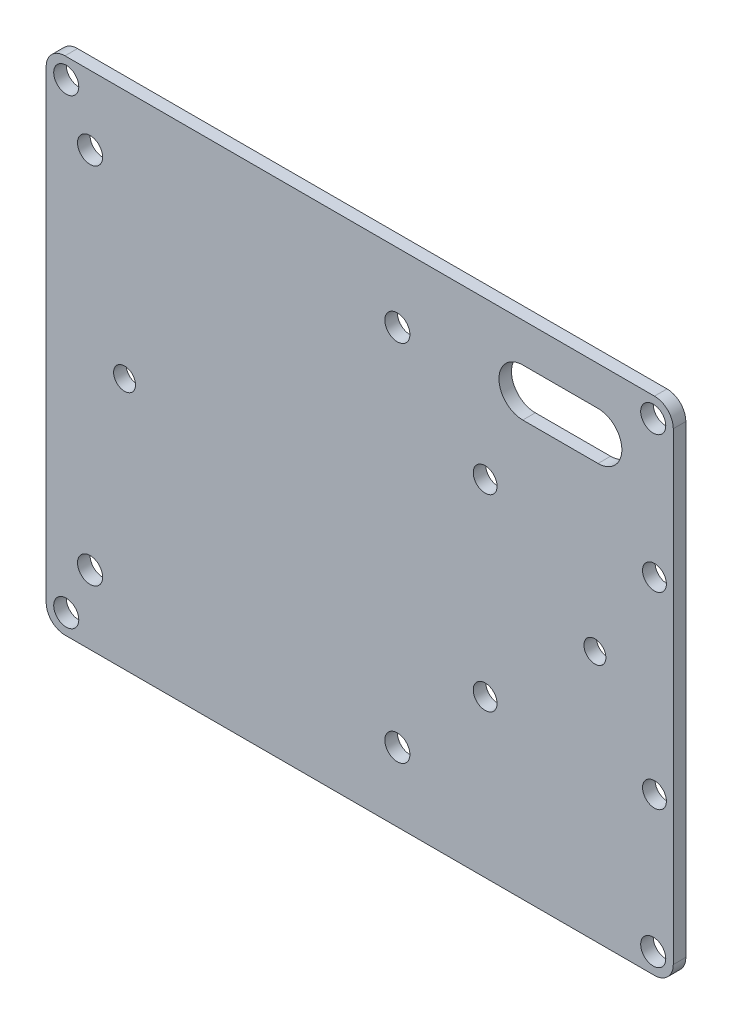
SolidWorks part; units mm, degrees
ref_plane "前视基准面" through (0, 0, 0) normal (0, 0, 1) x (1, 0, 0)
ref_plane "上视基准面" through (0, 0, 0) normal (0, 1, 0) x (1, 0, 0)
ref_plane "右视基准面" through (0, 0, 0) normal (1, 0, 0) x (0, 0, -1)
other "Configuration Table"
sketch "草图1" plane through (0, 0, 0) normal (0, 0, 1) x (1, 0, 0)
  line L1 (-47, 40) -> (47, 40)
  line L2 (-50, 37) -> (-50, -37)
  line L3 (-47, -40) -> (47, -40)
  line L4 (50, 37) -> (50, -37)
  line L5 (-50, 40) -> (50, -40) construction
  line L6 (-50, -40) -> (50, 40) construction
  arc A0 (-50, -37) -> (-47, -40) centre (-47, -37) ccw
  arc A1 (47, -40) -> (50, -37) centre (47, -37) ccw
  arc A2 (47, 40) -> (50, 37) centre (47, 37) cw
  arc A3 (-47, 40) -> (-50, 37) centre (-47, 37) ccw
  point P0 (0, 0)
  dimension "D3" = 3
  dimension "D1" = 100
  dimension "D2" = 80
extrude "凸台-拉伸1" add sketch "草图1" along normal blind 2
sketch "草图2" plane through (0, 0, 2) normal (0, 0, 1) x (1, 0, 0)
  line L0 (-50, 36.8) -> (50, 36.8) construction
  line L1 (-50, 37) -> (-50, -37) construction
  line L2 (50, -37) -> (50, 37) construction
  line L3 (-50, -36.8) -> (50, -36.8) construction
  line L4 (-46.8, 40) -> (-46.8, -40) construction
  line L5 (47, 40) -> (-47, 40) construction
  line L6 (-47, -40) -> (47, -40) construction
  line L7 (46.8, 40) -> (46.8, -40) construction
  line L8 (-50, 29) -> (50, 29) construction
  line L9 (-50, 0) -> (50, 0) construction
  line L10 (-50, -29) -> (50, -29) construction
  line L11 (47, 40) -> (47, -40) construction
  line L12 (-43, 40) -> (-43, -40) construction
  line L13 (6, 40) -> (6, -40.6054) construction
  line L14 (-50, 15) -> (50, 15) construction
  line L15 (-50, -15) -> (50, -15) construction
  line L16 (20, 40) -> (20, -40) construction
  circle A0 centre (-46.8, 36.8) radius 2
  circle A1 centre (46.8, 36.8) radius 2
  circle A2 centre (46.8, -36.8) radius 2
  circle A3 centre (-46.8, -36.8) radius 2
  circle A4 centre (-43, 29) radius 2
  circle A5 centre (6, 29) radius 2
  circle A6 centre (6, -29) radius 2
  circle A7 centre (-43, -29) radius 2
  circle A8 centre (47, -15) radius 1.9
  circle A10 centre (20, 15) radius 1.9
  circle A11 centre (20, -15) radius 1.9
  circle A13 centre (47, 15) radius 1.9
  point P16 (-46.8, 36.8)
  point P17 (46.8, 36.8)
  point P18 (46.8, -36.8)
  point P19 (-46.8, -36.8)
  point P34 (-43, 29)
  point P35 (6, 29)
  point P40 (6, -29)
  point P41 (-43, -29)
  point P56 (47, 15)
  point P57 (47, -15)
  point P64 (20, 15)
  point P65 (20, -15)
  dimension "D5" = 4
  dimension "D6" = 4
  dimension "D7" = 4
  dimension "D8" = 4
  dimension "D13" = 4
  dimension "D14" = 4
  dimension "D15" = 4
  dimension "D16" = 4
  dimension "D20" = 3.8
  dimension "D21" = 3.8
  dimension "D23" = 3.8
  dimension "D24" = 3.8
  dimension "D1" = 3.2
  dimension "D2" = 3.2
  dimension "D3" = 3.2
  dimension "D4" = 3.2
  dimension "D9" = 7
  dimension "D10" = 29
  dimension "D11" = 29
  dimension "D12" = 49
  dimension "D17" = 3
  dimension "D18" = 30
  dimension "D19" = 15
  dimension "D22" = 27
extrude "切除-拉伸1" cut sketch "草图2" against normal through all
sketch "草图3" plane through (0, 0, 2) normal (0, 0, 1) x (1, 0, 0)
  line L0 (-50, 30) -> (50, 30) construction
  line L1 (-50, 37) -> (-50, -37) construction
  line L2 (50, -37) -> (50, 37) construction
  line L3 (47, 40) -> (-47, 40) construction
  line L4 (32, 40) -> (32, -40) construction
  line L5 (-47, -40) -> (47, -40) construction
  line L6 (26, 30) -> (38, 30) construction
  line L7 (26, 33.8) -> (38, 33.8)
  line L8 (26, 26.2) -> (38, 26.2)
  arc A0 (26, 33.8) -> (26, 26.2) centre (26, 30) ccw
  arc A1 (38, 26.2) -> (38, 33.8) centre (38, 30) ccw
  point P12 (32, 30)
  point P15 (32, 30)
  dimension "D4" = 3.8
  dimension "D1" = 10
  dimension "D2" = 18
  dimension "D3" = 12
extrude "切除-拉伸2" cut sketch "草图3" against normal through all
sketch "草图4" plane through (0, 0, 2) normal (0, 0, 1) x (1, 0, 0)
  line L0 (-37.5, 40) -> (-37.5, -39.6609) construction
  line L1 (47, 40) -> (-47, 40) construction
  line L2 (37.5, 40) -> (37.5, -40) construction
  line L3 (-47, -40) -> (47, -40) construction
  line L4 (-50, 30) -> (50, 30) construction
  line L5 (-50, 37) -> (-50, -37) construction
  line L6 (50, -37) -> (50, 37) construction
  line L7 (-50, -30) -> (50, -30) construction
  circle A0 centre (-37.5, 0.1696) radius 1.75
  circle A1 centre (37.5, 0) radius 1.75
  dimension "D5" = 3.5
  dimension "D1" = 60
  dimension "D2" = 10
  dimension "D3" = 75
  dimension "D4" = 12.5
extrude "切除-拉伸3" cut sketch "草图4" against normal through all
